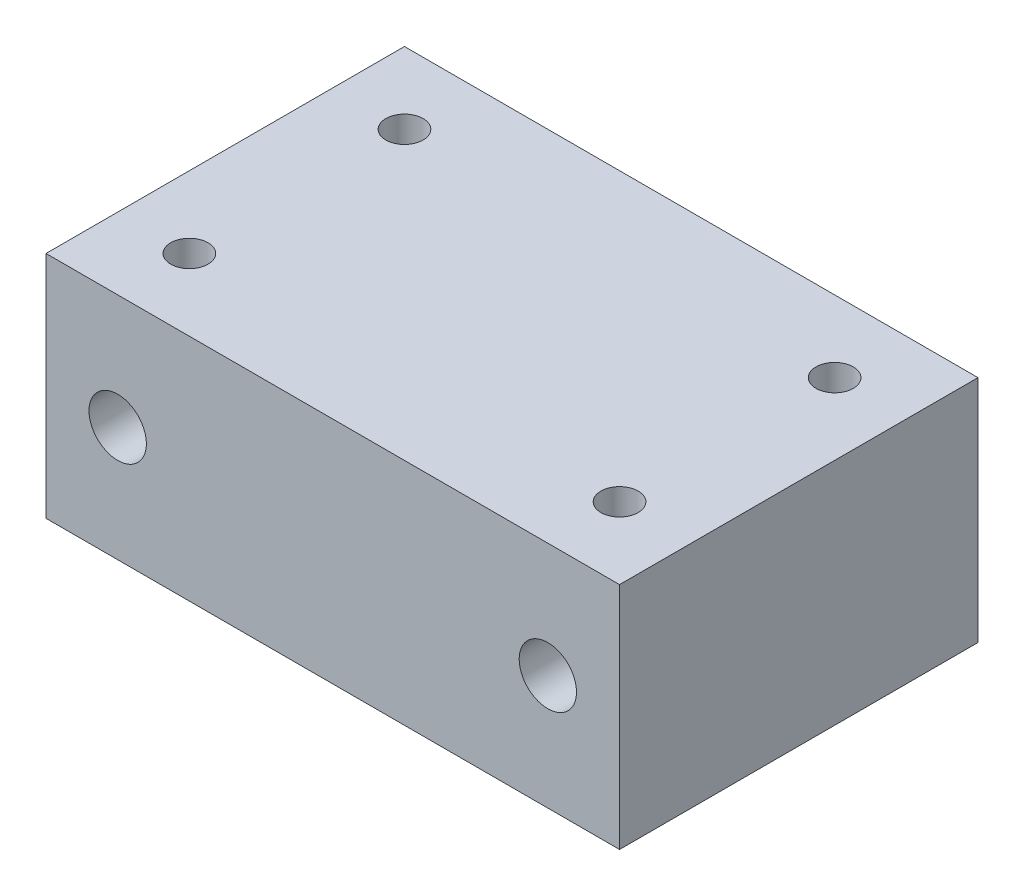
SolidWorks part; units mm, degrees
ref_plane "Front Plane" through (0, 0, 0) normal (0, 0, 1) x (1, 0, 0)
ref_plane "Top Plane" through (0, 0, 0) normal (0, 1, 0) x (1, 0, 0)
ref_plane "Right Plane" through (0, 0, 0) normal (1, 0, 0) x (0, 0, -1)
sketch "Sketch3" plane through (0, 0, 0) normal (0, 1, 0) x (1, 0, 0)
  line L1 (-40, 25) -> (40, 25)
  line L2 (-40, 25) -> (-40, -25)
  line L3 (-40, -25) -> (40, -25)
  line L4 (40, 25) -> (40, -25)
  dimension "D1" = 80
  dimension "D2" = 50
extrude "Boss-Extrude1" add sketch "Sketch3" along normal blind 32
sketch "Sketch4" plane through (0, 32, 0) normal (0, 1, 0) x (1, 0, 0)
  line L0 (0, 25) -> (0, -25) construction
  line L1 (40, 25) -> (-40, 25) construction
  line L2 (-40, -25) -> (40, -25) construction
  line L3 (40, 0) -> (-40, 0) construction
  line L4 (40, -25) -> (40, 25) construction
  line L5 (-40, 25) -> (-40, -25) construction
  circle A0 centre (-30, 15) radius 2.6
  circle A1 centre (30, 15) radius 2.6
  circle A2 centre (30, -15) radius 2.6
  circle A3 centre (-30, -15) radius 2.6
  dimension "D1" = 5.2
  dimension "D2" = 15
  dimension "D3" = 30
extrude "Cut-Extrude1" cut sketch "Sketch4" against normal blind 5
sketch "Sketch5" plane through (0, 0, -25) normal (0, 0, -1) x (-1, 0, 0)
  line L0 (40, 16) -> (-40, 16) construction
  line L1 (40, 32) -> (40, 0) construction
  line L2 (-40, 32) -> (-40, 0) construction
  circle A0 centre (-30, 16) radius 4
  circle A1 centre (30, 16) radius 4
  point P10 (0, 16)
  dimension "D1" = 8
  dimension "D2" = 8
  dimension "D3" = 60
  dimension "D4" = 30
extrude "Cut-Extrude2" cut sketch "Sketch5" against normal blind 65
